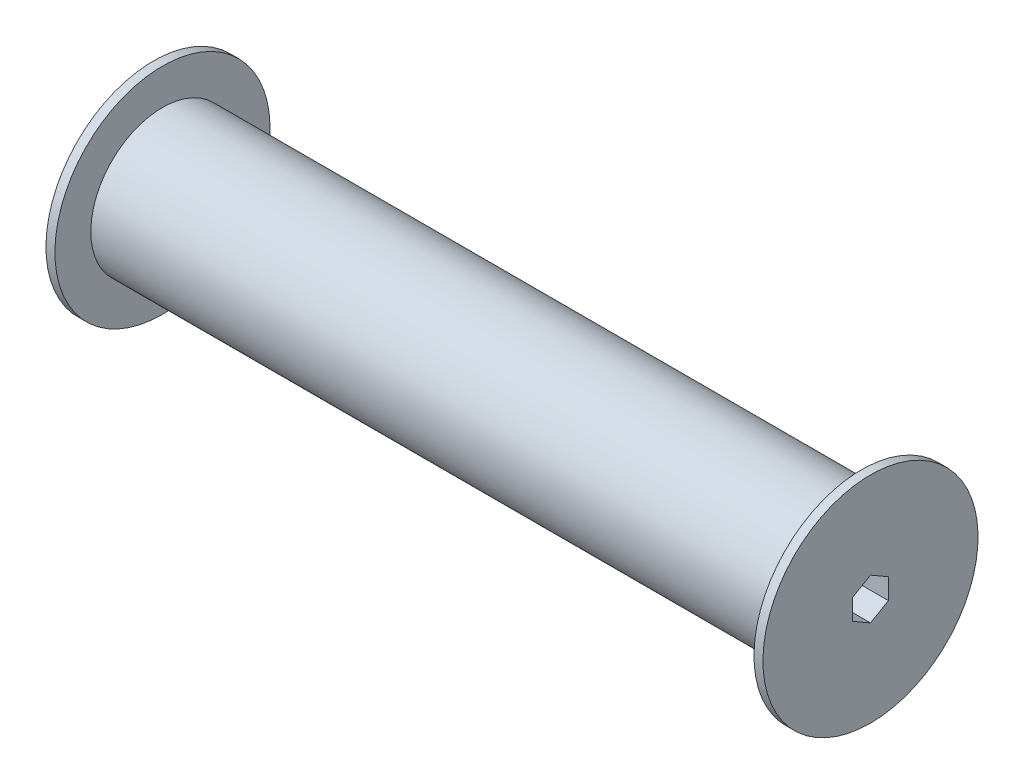
SolidWorks part; units mm, degrees
ref_plane "Front Plane" through (0, 0, 0) normal (0, 0, 1) x (1, 0, 0)
ref_plane "Top Plane" through (0, 0, 0) normal (0, 1, 0) x (1, 0, 0)
ref_plane "Right Plane" through (0, 0, 0) normal (1, 0, 0) x (0, 0, -1)
sketch "Sketch1" plane through (0, 0, 0) normal (0, 0, 1) x (1, 0, 0)
  line L0 (-127, 38.1) -> (-127, 0)
  line L1 (-127, 0) -> (127, 0)
  line L2 (127, 0) -> (127, 38.1)
  line L3 (123.825, 38.1) -> (123.825, 25.4)
  line L4 (123.825, 25.4) -> (-123.825, 25.4)
  line L5 (-123.825, 25.4) -> (-123.825, 38.1)
  line L6 (-123.825, 38.1) -> (-127, 38.1)
  line L7 (123.825, 38.1) -> (127, 38.1)
  point P12 (0, 0)
  dimension "D1" = 25.4
  dimension "D2" = 3.175
  dimension "D3" = 3.175
  dimension "D4" = 38.1
  dimension "D5" = 38.1
  dimension "D6" = 254
revolve "Revolve1" add sketch "Sketch1" angle 360 about L1
sketch "Sketch2" plane through (127, 0, 0) normal (1, 0, 0) x (0, 0, -1)
  line L1 (0, 7.3323) -> (-6.35, 3.6662)
  line L2 (-6.35, 3.6662) -> (-6.35, -3.6662)
  line L3 (-6.35, -3.6662) -> (0, -7.3323)
  line L4 (0, -7.3323) -> (6.35, -3.6662)
  line L5 (6.35, -3.6662) -> (6.35, 3.6662)
  line L6 (6.35, 3.6662) -> (0, 7.3323)
  circle A0 centre (0, 0) radius 6.35 construction
  dimension "D1" = 12.7
extrude "Cut-Extrude1" cut sketch "Sketch2" against normal through all
